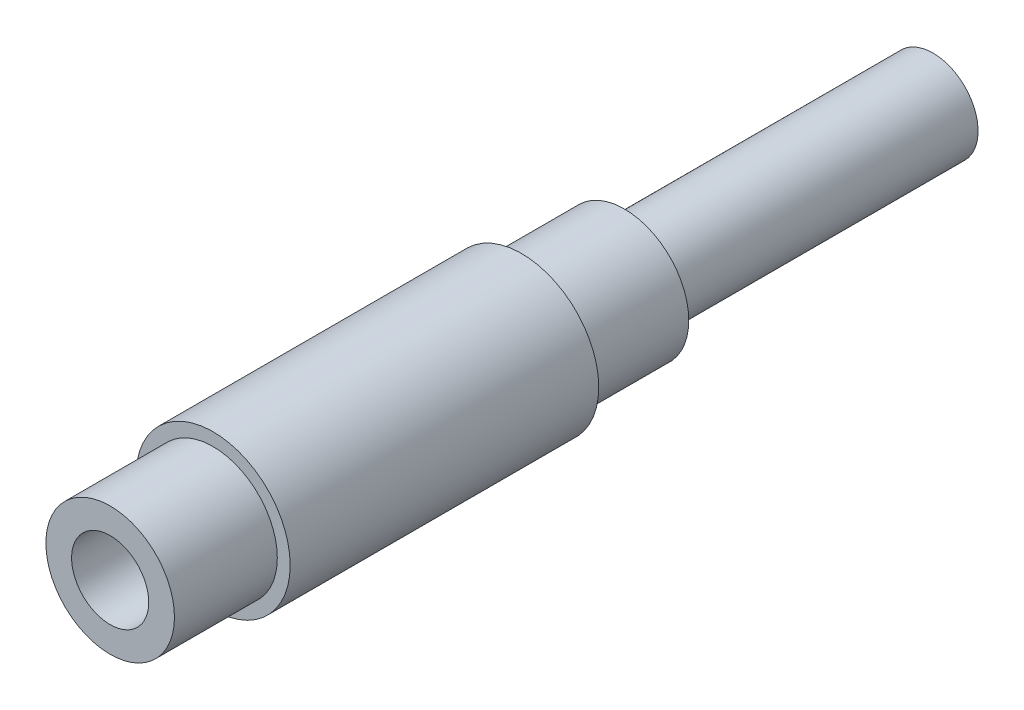
SolidWorks part; units mm, degrees
ref_plane "Front Plane" through (0, 0, 0) normal (0, 0, 1) x (1, 0, 0)
ref_plane "Top Plane" through (0, 0, 0) normal (0, 1, 0) x (1, 0, 0)
ref_plane "Right Plane" through (0, 0, 0) normal (1, 0, 0) x (0, 0, -1)
sketch "Sketch1" plane through (0, 0, 0) normal (0, 0, 1) x (1, 0, 0)
  circle A0 centre (0, 0) radius 7.9375
  dimension "D1" = 15.875
extrude "Boss-Extrude1" add sketch "Sketch1" along normal blind 63.5
sketch "Sketch4" plane through (0, 0, 0) normal (0, 0, -1) x (-1, 0, 0)
  circle A0 centre (0, 0) radius 5.5626
  dimension "D1" = 11.1252
extrude "Boss-Extrude2" add sketch "Sketch4" along normal blind 38.1
ref_plane "Plane1" through (0, 0, 12.7) normal (0, 0, 1) x (1, 0, 0)
sketch "Sketch6" plane through (0, 0, 12.7) normal (0, 0, 1) x (1, 0, 0)
  circle A0 centre (0, 0) radius 9.525
  circle A1 centre (0, 0) radius 7.9375
  circle A3 centre (0, 0) radius 7.9375 construction
  dimension "D1" = 19.05
extrude "Boss-Extrude4" add sketch "Sketch6" along normal offset from surface (38.1 mm away) 12.7 contours A0 up to face at (7.9375, 0, 63.5)
sketch "Sketch3" plane through (0, 0, 63.5) normal (0, 0, 1) x (1, 0, 0)
  circle A0 centre (0, 0) radius 4.7625
  dimension "D1" = 9.525
extrude "Cut-Extrude2" cut sketch "Sketch3" against normal blind 38.1
